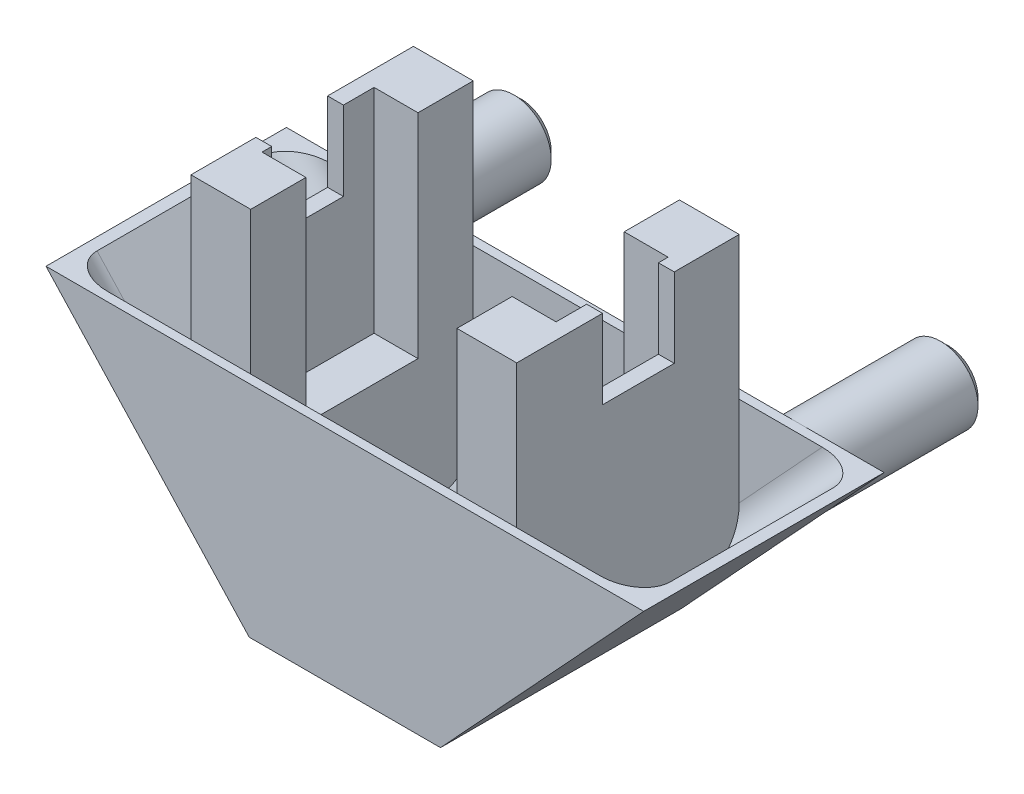
SolidWorks part; units mm, degrees
ref_plane "Ebene vorne" through (0, 0, 0) normal (0, 0, 1) x (1, 0, 0)
ref_plane "Ebene oben" through (0, 0, 0) normal (0, 1, 0) x (1, 0, 0)
ref_plane "Ebene rechts" through (0, 0, 0) normal (1, 0, 0) x (0, 0, -1)
sketch "Skizze4" plane through (0, 0, 0) normal (0, 0, 1) x (1, 0, 0)
  line L0 (-6.4, 0) -> (-20, 14.7)
  line L1 (-20, 14.7) -> (20, 14.7)
  line L2 (20, 14.7) -> (6.4, 0)
  line L3 (6.4, 0) -> (-6.4, 0)
  dimension "D1" = 12.8
  dimension "D2" = 40
  dimension "D3" = 14.7
extrude "Aufsatz-Linear austragen1" add sketch "Skizze4" along normal blind 16.09
shell "Wandung2" thickness 0.6
fillet "Verrundung1" radius 2 2 edges at (12.3826, 7.35, 15.49) (-12.3826, 7.35, 15.49)
fillet "Verrundung2" radius 2 2 edges at (12.3826, 7.35, 0.6) (-12.3826, 7.35, 0.6)
ref_plane "Ebene1" through (20, 0, 0) normal (1, 0, 0) x (0, 0, -1)
sketch "Skizze7" plane through (0, 0, 0) normal (0, 0, -1) x (-1, 0, 0)
  line L0 (-6.4, 0) -> (-20, 14.7) construction
  line L1 (-20, 14.7) -> (20, 14.7) construction
  line L2 (20, 14.7) -> (6.4, 0) construction
  circle A0 centre (-14.2813, 12.2) radius 2.5
  circle A1 centre (14.2813, 12.2) radius 2.5
  dimension "D1" = 5
extrude "Aufsatz-Linear austragen4" add sketch "Skizze7" along normal blind 10
chamfer "Fase3" distance 0.5 angle 45 2 edges at (11.7813, 12.2, -10) (-16.7813, 12.2, -10)
ref_plane "Ebene2" through (0, 4, 0) normal (0, 1, 0) x (1, 0, 0)
ref_plane "Ebene4" through (0, 0, 8.045) normal (0, 0, 1) x (1, 0, 0)
sketch "Skizze12" plane through (0, 0, 8.045) normal (0, 0, 1) x (1, 0, 0)
  line L0 (6.9, 0.5404) -> (6.9, 10)
  line L1 (6.4, 0) -> (20, 14.7) construction
  line L2 (6.9, 10) -> (10.9, 10)
  line L5 (-6.4, 0) -> (6.4, 0) construction
  line L6 (10.9, 10) -> (10.9, 4.864)
  line L7 (10.9, 4.864) -> (6.9, 0.5404)
  dimension "D1" = 0.5
  dimension "D2" = 10
  dimension "D3" = 4
extrude "Aufsatz-Linear austragen8" add sketch "Skizze12" along normal mid plane 15.7
ref_plane "Ebene5" through (9.84, 0, 0) normal (-1, 0, 0) x (0, 0, 1)
ref_plane "Ebene3" through (0, 0, 8.045) normal (0, 0, 1) x (1, 0, 0)
mirror "Spiegeln6" about plane through (0, 0, 0) normal (1, 0, 0) of "Aufsatz-Linear austragen8"
sketch "Skizze14" plane through (9.84, 0, 0) normal (-1, 0, 0) x (0, 0, 1)
  line L0 (15.49, 10) -> (0.6, 10) construction
  line L1 (4.295, 10) -> (0.6, 10)
  line L2 (4.295, 10) -> (4.295, 24.25)
  line L3 (4.295, 24.25) -> (0.6, 24.25)
  line L4 (0.6, 10) -> (0.6, 24.25)
  line L5 (15.49, 14.7) -> (15.49, 8.6925) construction
  line L6 (11.795, 10) -> (15.49, 10)
  line L7 (11.795, 10) -> (11.795, 24.25)
  line L8 (11.795, 24.25) -> (15.49, 24.25)
  line L9 (15.49, 10) -> (15.49, 24.25)
  line L10 (0.6, 10) -> (0.6, 4.369) construction
  dimension "D1" = 7.5
  dimension "D2" = 14.25
extrude "Aufsatz-Linear austragen9" add sketch "Skizze14" along normal up to vertex
sketch "Skizze15" plane through (9.84, 0, 0) normal (1, 0, 0) x (0, 0, -1)
  line L0 (-15.49, 14.7) -> (-15.49, 24.25) construction
  line L1 (-0.6, 24.25) -> (-15.49, 24.25)
  line L2 (-0.6, 24.25) -> (-0.6, 9.73)
  line L3 (-0.6, 9.73) -> (-15.49, 9.73)
  line L4 (-15.49, 24.25) -> (-15.49, 9.73)
  dimension "D1" = 14.52
extrude "Aufsatz-Linear austragen10" add sketch "Skizze15" along normal up to vertex (1.06 mm away)
sketch "Skizze16" plane through (9.84, 0, 0) normal (-1, 0, 0) x (0, 0, 1)
  line L0 (4.295, 24.25) -> (11.795, 24.25) construction
  line L1 (4.945, 24.25) -> (9.745, 24.25)
  line L2 (4.945, 24.25) -> (4.945, 18.95)
  line L3 (4.945, 18.95) -> (9.745, 18.95)
  line L4 (9.745, 24.25) -> (9.745, 18.95)
  line L5 (4.295, 10) -> (4.295, 24.25) construction
  dimension "D1" = 0.65
  dimension "D2" = 5.3
  dimension "D3" = 4.8
extrude "Schnitt-Linear austragen1" cut sketch "Skizze16" against normal up to next
mirror "Spiegeln9" about plane through (0, 0, 0) normal (1, 0, 0) of "Aufsatz-Linear austragen9"
sketch "Skizze17" plane through (-9.84, 0, 0) normal (-1, 0, 0) x (0, 0, 1)
  line L1 (15.49, 9.73) -> (0.6, 9.73)
  line L2 (15.49, 9.73) -> (15.49, 24.25)
  line L3 (15.49, 24.25) -> (0.6, 24.25)
  line L4 (0.6, 9.73) -> (0.6, 24.25)
  dimension "D1" = 14.52
extrude "Aufsatz-Linear austragen11" add sketch "Skizze17" along normal up to vertex (1.06 mm away)
sketch "Skizze18" plane through (-9.84, 0, 0) normal (1, 0, 0) x (0, 0, -1)
  line L0 (-11.145, 24.25) -> (-11.145, 18.95)
  line L1 (-9.745, 24.25) -> (-15.49, 24.25) construction
  line L2 (-11.145, 18.95) -> (-6.345, 18.95)
  line L3 (-9.745, 18.95) -> (-4.945, 18.95) construction
  line L4 (-6.345, 18.95) -> (-6.345, 24.25)
  line L5 (-11.795, 24.25) -> (-4.295, 24.25) construction
  line L6 (-6.345, 24.25) -> (-11.145, 24.25)
  line L7 (-11.795, 24.25) -> (-11.795, 10) construction
  dimension "D1" = 5.3
  dimension "D2" = 4.8
  dimension "D3" = 0.65
extrude "Schnitt-Linear austragen2" cut sketch "Skizze18" against normal up to next
